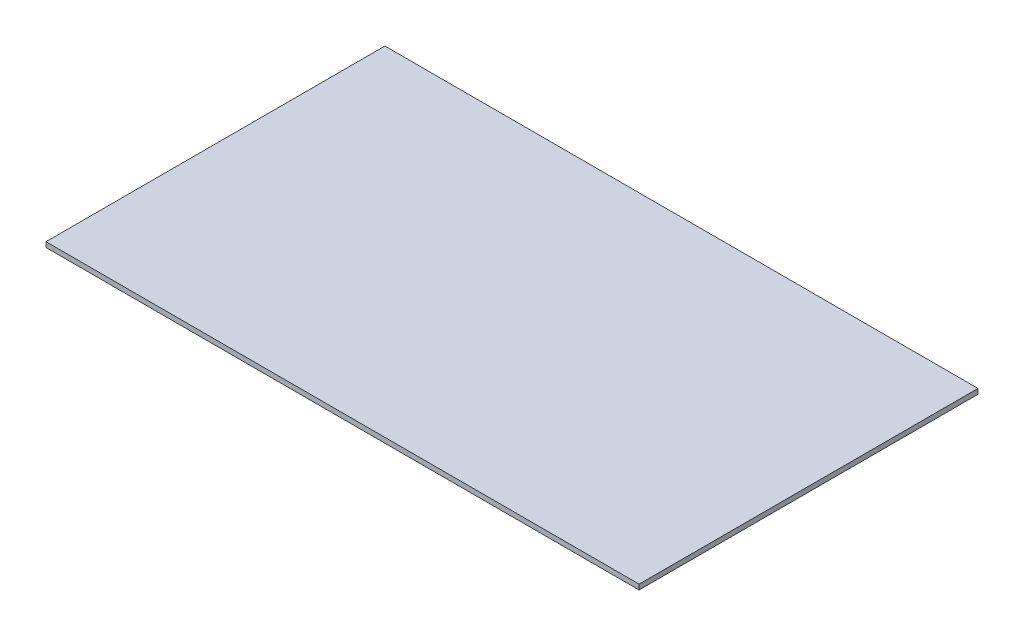
SolidWorks part; units mm, degrees
ref_plane "Front Plane" through (0, 0, 0) normal (0, 0, 1) x (1, 0, 0)
ref_plane "Top Plane" through (0, 0, 0) normal (0, 1, 0) x (1, 0, 0)
ref_plane "Right Plane" through (0, 0, 0) normal (1, 0, 0) x (0, 0, -1)
sketch "Sketch1" plane through (0, 0, 0) normal (0, 1, 0) x (1, 0, 0)
  line L1 (0, 0) -> (350, 0)
  line L2 (0, 0) -> (0, 200)
  line L3 (0, 200) -> (350, 200)
  line L4 (350, 0) -> (350, 200)
extrude "Boss-Extrude1" add sketch "Sketch1" along normal blind 3
